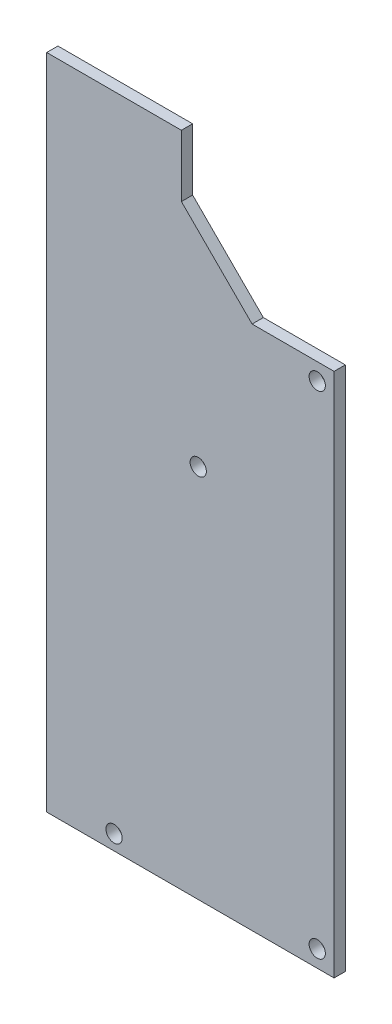
SolidWorks part; units mm, degrees
ref_plane "Front Plane" through (0, 0, 0) normal (0, 0, 1) x (1, 0, 0)
ref_plane "Top Plane" through (0, 0, 0) normal (0, 1, 0) x (1, 0, 0)
ref_plane "Right Plane" through (0, 0, 0) normal (1, 0, 0) x (0, 0, -1)
sketch "Sketch1" plane through (0, 0, 0) normal (0, 0, 1) x (1, 0, 0)
  line L4 (-0.1587, -5.3083) -> (6.1913, -5.3083) construction
  line L5 (-6.5087, -5.3083) -> (12.5413, -5.3083)
  line L6 (-6.5087, -5.3083) -> (-6.5087, 83.5917)
  line L7 (-6.5087, 83.5917) -> (12.5413, 83.5917)
  line L8 (12.5413, -5.3083) -> (12.5413, 83.5917)
  line L9 (-6.5087, -5.3083) -> (12.5413, 83.5917) construction
  line L10 (-6.5087, 83.5917) -> (12.5413, -5.3083) construction
  line L11 (15.8433, 83.5917) -> (-6.0007, 83.5917) construction
  line L30 (-6.5087, 83.0837) -> (-6.5087, -8.6103) construction
  line L31 (12.5413, -8.6103) -> (12.5413, 77.2417) construction
  point P4 (3.0163, 39.1417)
extrude "Boss-Extrude1" add sketch "Sketch1" along normal blind 1.5875
hole_wizard "#0 Clearance Hole1" positions "Sketch3" profile "Sketch2" hole size "#0" standard "ANSI Inch"
sketch "Sketch3" plane through (0, 0, 1.5875) normal (0, 0, 1) x (1, 0, 0)
  line L0 (10.5728, 11.7732) -> (12.5413, 14.1227) construction
  line L1 (12.5413, -5.3083) -> (12.5413, 83.5917) construction
  line L3 (10.5728, 64.1607) -> (12.5413, 66.5102) construction
  line L5 (3.0163, 83.5917) -> (3.0163, -5.3083) construction
  line L6 (12.5413, 83.5917) -> (-6.5087, 83.5917) construction
  line L7 (-6.5087, -5.3083) -> (12.5413, -5.3083) construction
  line L9 (-4.5402, 64.1607) -> (-6.5087, 66.5102) construction
  line L10 (-4.5402, 11.7732) -> (-6.5087, 14.1227) construction
  point P24 (-5.5245, 65.3355)
  point P26 (11.557, 65.3355)
  point P28 (11.557, 12.948)
  point P30 (-5.5245, 12.948)
sketch "Sketch2" plane through (-5.5245, 65.3355, 1.5875) normal (1, 0, 0) x (0, -1, 0)
  line L0 (0, 0) -> (0, 1.5875)
  line L1 (0, 1.5875) -> (0.9271, 1.5875)
  line L2 (0.9271, 1.5875) -> (0.9271, 0)
  line L5 (0.9271, 0) -> (0, 0)
  line L11 (0, -6.35) -> (0, 107.95) construction
  dimension "Thru Hole Dia." = 1.8542
  dimension "Thru Hole Depth" = 1.5875
sketch "Sketch4" plane through (0, 0, 1.5875) normal (0, 0, 1) x (1, 0, 0)
  line L0 (36.6713, 91.3387) -> (36.6713, -28.2953) construction
  line L1 (12.5413, -5.3083) -> (34.1313, -5.3083)
  line L2 (12.5413, -5.3083) -> (12.5413, 66.4467)
  line L3 (12.5413, 66.4467) -> (34.1313, 66.4467)
  line L4 (34.1313, -5.3083) -> (34.1313, 66.4467)
  circle A0 centre (23.9713, 75.9717) radius 0.7874 construction
  dimension "D1" = 2.54
  dimension "D2" = 9.525
extrude "Boss-Extrude2" add sketch "Sketch4" against normal through all
chamfer "Chamfer1" distance 10 angle 45 1 edges at (12.5413, 66.4467, 0.7937)
sketch "Sketch5" plane through (0, 0, 1.5875) normal (0, 0, 1) x (1, 0, 0)
  line L0 (-6.5087, 83.5917) -> (-6.5087, -5.3083) construction
  line L1 (34.1313, -5.3083) -> (-6.5087, -5.3083)
  line L2 (34.1313, -5.3083) -> (34.1313, -7.8483)
  line L3 (34.1313, -7.8483) -> (-6.5087, -7.8483)
  line L4 (-6.5087, -5.3083) -> (-6.5087, -7.8483)
  line L6 (12.5413, 83.5917) -> (-6.5087, 83.5917)
  line L7 (12.5413, 83.5917) -> (12.5413, 85.1792)
  line L8 (12.5413, 85.1792) -> (-6.5087, 85.1792)
  line L9 (-6.5087, 83.5917) -> (-6.5087, 85.1792)
  dimension "D1" = 2.54
  dimension "D2" = 1.5875
extrude "Boss-Extrude3" add sketch "Sketch5" against normal through all
hole_wizard "Ø2.3 (2.3) Diameter Hole1" positions "Sketch6" profile "Sketch7" hole size "Ø2.3" standard "ANSI Metric" end condition through all
sketch "Sketch6" plane through (0, 0, 1.5875) normal (0, 0, 1) x (1, 0, 0)
  point P0 (14.9225, 45.1655)
  point P6 (31.75, 64.0655)
  point P9 (31.75, -5.467)
  point P14 (3.0162, -5.721)
sketch "Sketch7" plane through (14.9225, 45.1655, 1.5875) normal (1, 0, 0) x (0, -1, 0)
  line L0 (0, 0) -> (0, 1.5875)
  line L1 (0, 1.5875) -> (1.15, 1.5875)
  line L2 (1.15, 1.5875) -> (1.15, 0)
  line L5 (1.15, 0) -> (0, 0)
  line L11 (0, -6.35) -> (0, 107.95) construction
  dimension "Thru Hole Dia." = 2.3
  dimension "Thru Hole Depth" = 1.5875
